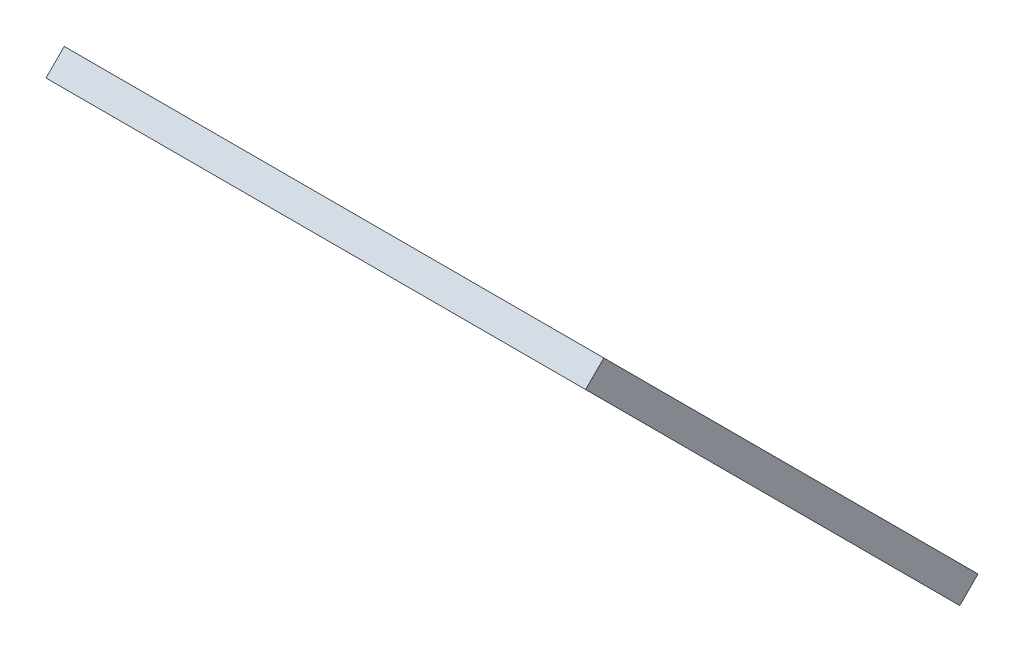
SolidWorks part; units mm, degrees
material "Acrylic (Medium-high impact)"
ref_plane "Front Plane" through (0, 0, 0) normal (0, 0, 1) x (1, 0, 0)
ref_plane "Top Plane" through (0, 0, 0) normal (0, 1, 0) x (1, 0, 0)
ref_plane "Right Plane" through (0, 0, 0) normal (1, 0, 0) x (0, 0, -1)
ref_plane "Plane1" through (0, -80.4015, 80.4015) normal (0, -0.7071, 0.7071) x (-1, 0, 0)
sketch "Sketch1" plane through (0, -80.4015, 80.4015) normal (0, -0.7071, 0.7071) x (-1, 0, 0)
  line L0 (-111.1649, 111.1649) -> (-111.1649, 49.6381) construction
  line L1 (-4.9069, 111.1649) -> (-111.1649, 111.1649) construction
  line L2 (-111.1649, 49.6381) -> (-48.4129, 49.6381) construction
  line L3 (-48.4129, 49.6381) -> (-4.9069, 111.1649) construction
  line L4 (-111.1649, 111.1649) -> (-111.1649, 49.6381)
  line L5 (-4.9069, 111.1649) -> (-111.1649, 111.1649)
  line L6 (-111.1649, 49.6381) -> (-48.4129, 49.6381)
  line L7 (-48.4129, 49.6381) -> (-4.9069, 111.1649)
extrude "Boss-Extrude1" add sketch "Sketch1" along normal mid plane 3
